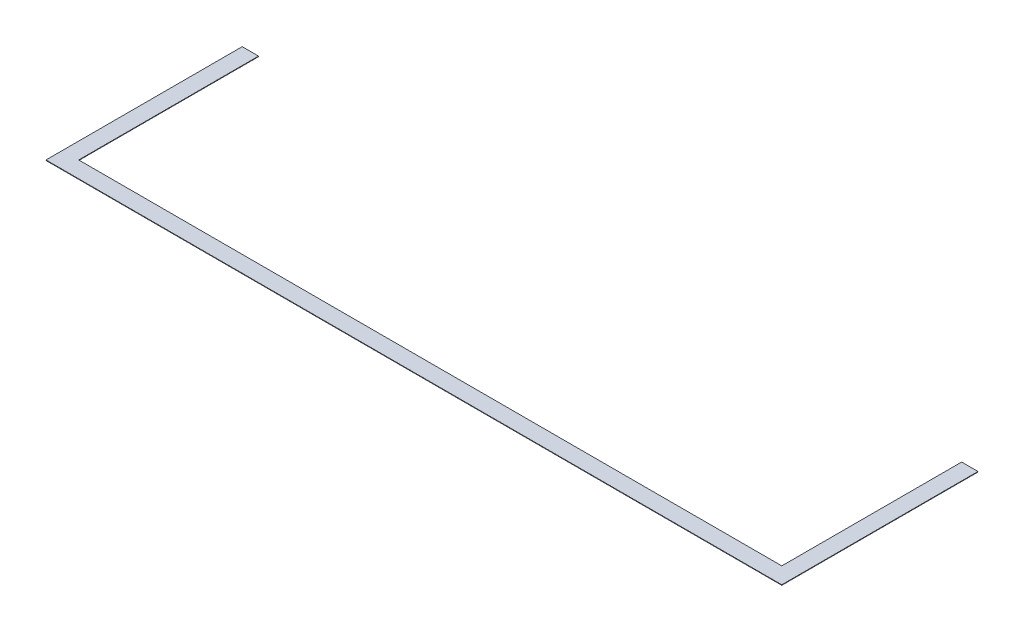
SolidWorks part; units mm, degrees
ref_plane "Front Plane" through (0, 0, 0) normal (0, 0, 1) x (1, 0, 0)
ref_plane "Top Plane" through (0, 0, 0) normal (0, 1, 0) x (1, 0, 0)
ref_plane "Right Plane" through (0, 0, 0) normal (1, 0, 0) x (0, 0, -1)
sketch "Sketch1" plane through (0, 0, 0) normal (0, 1, 0) x (1, 0, 0)
  line L0 (0, 0) -> (0, -609.6)
  line L1 (0, -609.6) -> (2286, -609.6)
  line L2 (2286, -609.6) -> (2286, 0)
  line L3 (2286, 0) -> (2235.2, 0)
  line L4 (2235.2, 0) -> (2235.2, -558.8)
  line L5 (2235.2, -558.8) -> (50.8, -558.8)
  line L6 (50.8, -558.8) -> (50.8, 0)
  line L7 (50.8, 0) -> (0, 0)
  line L8 (50.8, -558.8) -> (50.8, -609.6) construction
  dimension "D1" = 50.8
  dimension "D2" = 2286
  dimension "D3" = 609.6
extrude "Boss-Extrude1" add sketch "Sketch1" along normal blind 1.5875 contours L8 L6 L7 L0 L1 | L5 L8 L1 L2 L3 L4
